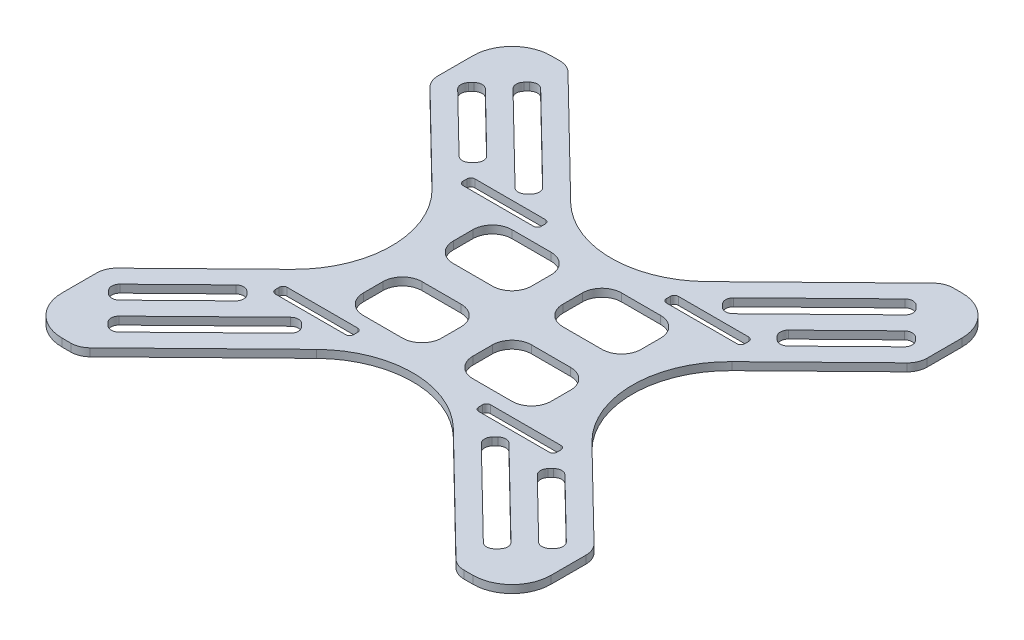
SolidWorks part; units mm, degrees
ref_plane "前视基准面" through (0, 0, 0) normal (0, 0, 1) x (1, 0, 0)
ref_plane "上视基准面" through (0, 0, 0) normal (0, 1, 0) x (1, 0, 0)
ref_plane "右视基准面" through (0, 0, 0) normal (1, 0, 0) x (0, 0, -1)
sketch "草图1" plane through (0, 0, 0) normal (0, 1, 0) x (1, 0, 0)
  line L0 (0, -9.1053) -> (0, -15.8579) construction
  line L1 (-62.5, -62.5) -> (62.5, -62.5)
  line L2 (-62.5, -62.5) -> (-62.5, 62.5)
  line L3 (-62.5, 62.5) -> (62.5, 62.5)
  line L4 (62.5, -62.5) -> (62.5, 62.5)
  line L5 (-62.5, -62.5) -> (62.5, 62.5) construction
  line L6 (-62.5, 62.5) -> (62.5, -62.5) construction
  line L7 (12.1957, 0) -> (23.1686, 0) construction
  line L8 (36, 25.5) -> (16, 25.5)
  line L9 (-36, 22.5) -> (-16, 22.5)
  line L10 (-36, 22.5) -> (-36, 25.5)
  line L11 (-36, 25.5) -> (-16, 25.5)
  line L12 (-16, 22.5) -> (-16, 25.5)
  line L13 (-36, 22.5) -> (-16, 25.5) construction
  line L14 (-36, 25.5) -> (-16, 22.5) construction
  line L15 (16, 22.5) -> (16, 25.5)
  line L16 (36, 22.5) -> (16, 22.5)
  line L17 (36, 22.5) -> (36, 25.5)
  line L18 (36, -22.5) -> (36, -25.5)
  line L19 (36, -22.5) -> (16, -22.5)
  line L20 (16, -22.5) -> (16, -25.5)
  line L21 (36, -25.5) -> (16, -25.5)
  line L22 (-36, -25.5) -> (-16, -25.5)
  line L23 (-16, -22.5) -> (-16, -25.5)
  line L24 (-36, -22.5) -> (-16, -22.5)
  line L25 (-36, -22.5) -> (-36, -25.5)
  point P0 (0, 0)
  point P7 (-26, 24)
  dimension "D1" = 125
  dimension "D2" = 125
  dimension "D3" = 20
  dimension "D4" = 3
  dimension "D5" = 32
  dimension "D6" = 45
extrude "凸台-拉伸1" add sketch "草图1" along normal blind 2
fillet "圆角1" radius 1 16 edges at (-16, 1, -22.5) (36, 1, -22.5) (-16, 1, 25.5) (36, 1, 25.5) (16, 1, 25.5) (-36, 1, 25.5) (-36, 1, -22.5) (16, 1, -22.5) (-16, 1, -25.5) (36, 1, -25.5) (36, 1, 22.5) (-16, 1, 22.5) (-36, 1, 22.5) (16, 1, 22.5) (16, 1, -25.5) (-36, 1, -25.5)
sketch "草图2" plane through (0, 2, 0) normal (0, 1, 0) x (1, 0, 0)
  line L0 (-62.5, 41.5) -> (-20, 0)
  line L1 (-62.5, 62.5) -> (-62.5, -62.5) construction
  line L2 (-20, 0) -> (-62.5, -41.5)
  line L3 (9.9754, 0) -> (30.9804, 0) construction
  line L4 (0, -8.5901) -> (0, -26.3385) construction
  line L5 (-62.5, 41.5) -> (-62.5, -41.5)
  line L6 (62.5, 62.5) -> (-62.5, 62.5) construction
  line L7 (62.5, 41.5) -> (20, 0)
  line L8 (20, 0) -> (62.5, -41.5)
  line L9 (62.5, 41.5) -> (62.5, -41.5)
  line L10 (-48.2222, 62.5) -> (0, 15.4125)
  line L11 (0, 15.4125) -> (48.2222, 62.5)
  line L12 (48.2222, 62.5) -> (-48.2222, 62.5)
  line L13 (0, -15.4125) -> (48.2222, -62.5)
  line L14 (-48.2222, -62.5) -> (0, -15.4125)
  line L15 (48.2222, -62.5) -> (-48.2222, -62.5)
  dimension "D1" = 20
  dimension "D2" = 21
  dimension "D3" = 25
extrude "切除-拉伸1" cut sketch "草图2" against normal through all
fillet "圆角2" radius 25 4 edges at (0, 1, 15.4125) (-20, 1, 0) (20, 1, 0) (0, 1, -15.4125)
fillet "圆角3" radius 10 4 edges at (62.5, 1, -62.5) (-62.5, 1, -62.5) (62.5, 1, 62.5) (-62.5, 1, 62.5)
fillet "圆角4" radius 5 4 edges at (62.5, 1, -41.5) (62.5, 1, 41.5) (-62.5, 1, 41.5) (-62.5, 1, -41.5)
fillet "圆角5" radius 5 4 edges at (-48.2222, 1, 62.5) (48.2222, 1, 62.5) (48.2222, 1, -62.5) (-48.2222, 1, -62.5)
sketch "草图3" plane through (0, 2, 0) normal (0, 1, 0) x (1, 0, 0)
  line L0 (-51.512, 51.7356) -> (-26.4704, 27.2832)
  line L5 (0, -2.3882) -> (0, -8.7036) construction
  line L6 (7.7883, 0) -> (15.4363, 0) construction
  line L7 (-58.4983, 44.5809) -> (-40.6115, 27.1149)
  line L13 (24, 19) -> (4, 19)
  line L14 (-24, 4) -> (-4, 4)
  line L22 (-40.6115, 27.1149) -> (-37.1183, 30.6923)
  line L23 (-37.1183, 30.6923) -> (-55.0051, 48.1582)
  line L24 (-26.4704, 27.2832) -> (-22.9772, 30.8606)
  line L25 (-55.0051, 48.1582) -> (-58.4983, 44.5809)
  line L26 (-38.3179, 17.8869) -> (-60.9932, 40.0287) construction
  line L27 (-46.7653, 61.0774) -> (-17.466, 32.4675) construction
  line L28 (-22.9772, 30.8606) -> (-48.0188, 55.313)
  line L29 (-48.0188, 55.313) -> (-51.512, 51.7356)
  line L30 (48.0188, 55.313) -> (51.512, 51.7356)
  line L31 (22.9772, 30.8606) -> (48.0188, 55.313)
  line L32 (26.4704, 27.2832) -> (22.9772, 30.8606)
  line L33 (51.512, 51.7356) -> (26.4704, 27.2832)
  line L34 (37.1183, 30.6923) -> (55.0051, 48.1582)
  line L35 (40.6115, 27.1149) -> (37.1183, 30.6923)
  line L36 (58.4983, 44.5809) -> (40.6115, 27.1149)
  line L37 (55.0051, 48.1582) -> (58.4983, 44.5809)
  line L38 (-37.1183, -30.6923) -> (-55.0051, -48.1582)
  line L39 (-40.6115, -27.1149) -> (-37.1183, -30.6923)
  line L40 (-58.4983, -44.5809) -> (-40.6115, -27.1149)
  line L41 (-55.0051, -48.1582) -> (-58.4983, -44.5809)
  line L42 (-48.0188, -55.313) -> (-51.512, -51.7356)
  line L43 (-22.9772, -30.8606) -> (-48.0188, -55.313)
  line L44 (-26.4704, -27.2832) -> (-22.9772, -30.8606)
  line L45 (-51.512, -51.7356) -> (-26.4704, -27.2832)
  line L46 (40.6115, -27.1149) -> (37.1183, -30.6923)
  line L47 (58.4983, -44.5809) -> (40.6115, -27.1149)
  line L48 (55.0051, -48.1582) -> (58.4983, -44.5809)
  line L49 (37.1183, -30.6923) -> (55.0051, -48.1582)
  line L50 (22.9772, -30.8606) -> (48.0188, -55.313)
  line L51 (26.4704, -27.2832) -> (22.9772, -30.8606)
  line L52 (51.512, -51.7356) -> (26.4704, -27.2832)
  line L53 (48.0188, -55.313) -> (51.512, -51.7356)
  line L54 (-24, 4) -> (-24, 19)
  line L55 (-24, 19) -> (-4, 19)
  line L56 (-4, 4) -> (-4, 19)
  line L57 (-24, 4) -> (-4, 19) construction
  line L58 (-24, 19) -> (-4, 4) construction
  line L59 (4, 4) -> (4, 19)
  line L60 (24, 4) -> (4, 4)
  line L61 (24, 4) -> (24, 19)
  line L62 (24, -4) -> (24, -19)
  line L63 (24, -4) -> (4, -4)
  line L64 (4, -4) -> (4, -19)
  line L65 (24, -19) -> (4, -19)
  line L66 (-24, -19) -> (-4, -19)
  line L67 (-4, -4) -> (-4, -19)
  line L68 (-24, -4) -> (-4, -4)
  line L69 (-24, -4) -> (-24, -19)
  point P0 (0, 0)
  point P4 (-14, 11.5)
  dimension "D1" = 20
  dimension "D2" = 8
  dimension "D3" = 8
  dimension "D4" = 5
  dimension "D5" = 5
  dimension "D6" = 48
  dimension "D7" = 25
  dimension "D8" = 5
  dimension "D9" = 10
  dimension "D10" = 15
extrude "切除-拉伸2" cut sketch "草图3" against normal through all
fillet "圆角7" radius 5 16 edges at (-4, 1, 19) (-4, 1, -4) (24, 1, -4) (24, 1, 19) (4, 1, -19) (4, 1, 4) (-24, 1, 4) (-24, 1, 19) (4, 1, 19) (4, 1, -4) (-24, 1, -4) (-4, 1, 4) (24, 1, 4) (24, 1, -19) (-4, 1, -19) (-24, 1, -19)
fillet "圆角8" radius 2 32 edges at (-22.9772, 1, -30.8606) (-37.1183, 1, -30.6923) (-26.4704, 1, -27.2832) (-40.6115, 1, -27.1149) (-51.512, 1, -51.7356) (-48.0188, 1, -55.313) (-55.0051, 1, -48.1582) (-58.4983, 1, -44.5809) (40.6115, 1, -27.1149) (26.4704, 1, -27.2832) (22.9772, 1, -30.8606) (37.1183, 1, -30.6923) (58.4983, 1, -44.5809) (51.512, 1, -51.7356) (55.0051, 1, -48.1582) (48.0188, 1, -55.313) (51.512, 1, 51.7356) (58.4983, 1, 44.5809) (55.0051, 1, 48.1582) (48.0188, 1, 55.313) (37.1183, 1, 30.6923) (22.9772, 1, 30.8606) (40.6115, 1, 27.1149) (26.4704, 1, 27.2832) (-26.4704, 1, 27.2832) (-40.6115, 1, 27.1149) (-48.0188, 1, 55.313) (-55.0051, 1, 48.1582) (-51.512, 1, 51.7356) (-58.4983, 1, 44.5809) (-22.9772, 1, 30.8606) (-37.1183, 1, 30.6923)
